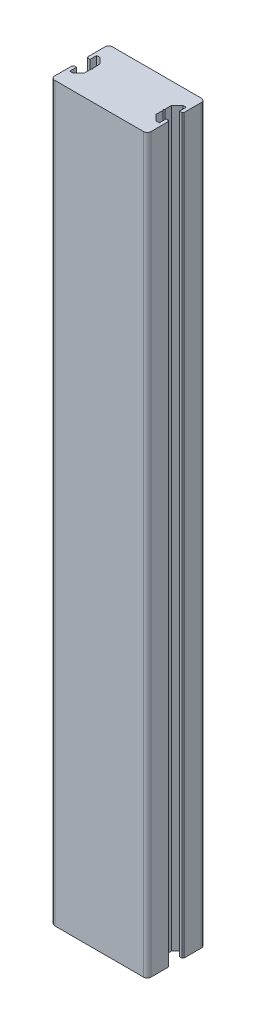
SolidWorks part; units mm, degrees
ref_plane "Front Plane" through (0, 0, 0) normal (0, 0, 1) x (1, 0, 0)
ref_plane "Top Plane" through (0, 0, 0) normal (0, 1, 0) x (1, 0, 0)
ref_plane "Right Plane" through (0, 0, 0) normal (1, 0, 0) x (0, 0, -1)
sketch "Sketch1" plane through (0, 0, 0) normal (0, 1, 0) x (1, 0, 0)
  line L0 (0, 17.25) -> (2.625, 17.25)
  line L5 (0, 0) -> (75, 0)
  line L6 (0, 0) -> (0, 45)
  line L7 (0, 45) -> (75, 45)
  line L8 (75, 0) -> (75, 45)
  line L9 (2.625, 17.25) -> (2.625, 12)
  line L10 (2.625, 12) -> (5.25, 12)
  line L11 (5.25, 12) -> (9.625, 16.375)
  line L12 (9.625, 16.375) -> (9.625, 28.625)
  line L13 (9.625, 28.625) -> (5.25, 33)
  line L14 (5.25, 33) -> (2.625, 33)
  line L15 (2.625, 33) -> (2.625, 27.75)
  line L16 (2.625, 27.75) -> (0, 27.75)
  line L17 (0, 27.75) -> (0, 17.25)
  line L18 (37.5, 45) -> (37.5, 0) construction
  line L19 (72.375, 27.75) -> (75, 27.75)
  line L20 (72.375, 33) -> (72.375, 27.75)
  line L21 (69.75, 33) -> (72.375, 33)
  line L22 (65.375, 28.625) -> (69.75, 33)
  line L23 (65.375, 16.375) -> (65.375, 28.625)
  line L24 (69.75, 12) -> (65.375, 16.375)
  line L25 (72.375, 12) -> (69.75, 12)
  line L26 (72.375, 17.25) -> (72.375, 12)
  line L27 (75, 17.25) -> (72.375, 17.25)
  line L28 (75, 27.75) -> (75, 17.25)
  line L29 (0, 17.25) -> (0.75, 17.25)
  line L30 (0, 16.5) -> (0, 17.25)
  line L31 (0, 27.75) -> (0.75, 27.75)
  line L32 (0, 28.5) -> (0, 27.75)
  line L33 (75, 16.5) -> (75, 17.25)
  line L34 (75, 17.25) -> (74.25, 17.25)
  line L35 (75, 28.5) -> (75, 27.75)
  line L36 (75, 27.75) -> (74.25, 27.75)
  line L37 (9.625, 23.25) -> (10.375, 22.5)
  line L38 (10.375, 22.5) -> (9.625, 21.75)
  line L39 (9.625, 21.75) -> (9.625, 23.25)
  line L40 (64.625, 22.5) -> (65.375, 21.75)
  line L41 (65.375, 23.25) -> (64.625, 22.5)
  line L42 (65.375, 21.75) -> (65.375, 23.25)
  arc A0 (0.75, 27.75) -> (0, 28.5) centre (0, 27.75) ccw
  arc A1 (0.75, 17.25) -> (0, 16.5) centre (0, 17.25) cw
  arc A2 (74.25, 17.25) -> (75, 16.5) centre (75, 17.25) ccw
  arc A3 (74.25, 27.75) -> (75, 28.5) centre (75, 27.75) cw
  point P8 (9.625, 22.5)
  point P17 (0, 22.5)
  dimension "D9" = 0.75
  dimension "D10" = 0.75
  dimension "D1" = 45
  dimension "D2" = 75
  dimension "D3" = 10.5
  dimension "D4" = 12.25
  dimension "D5" = 9.625
  dimension "D6" = 2.625
  dimension "D7" = 2.625
  dimension "D8" = 21
  dimension "D11" = 0.75
  dimension "D12" = 0.75
  dimension "D13" = 0.75
extrude "Boss-Extrude1" add sketch "Sketch1" along normal blind 570 contours L18 L7 L6 A0 L16 L15 L14 L13 L12 L37 L38 L11 L10 L9 L0 A1 L5 | L7 L18 L5 L8 A2 L27 L26 L25 L24 L23 L40 L41 L22 L21 L20 L19 A3
fillet "Fillet1" radius 3 4 edges at (75, 285, 0) (0, 285, 0) (0, 285, -45) (75, 285, -45)
